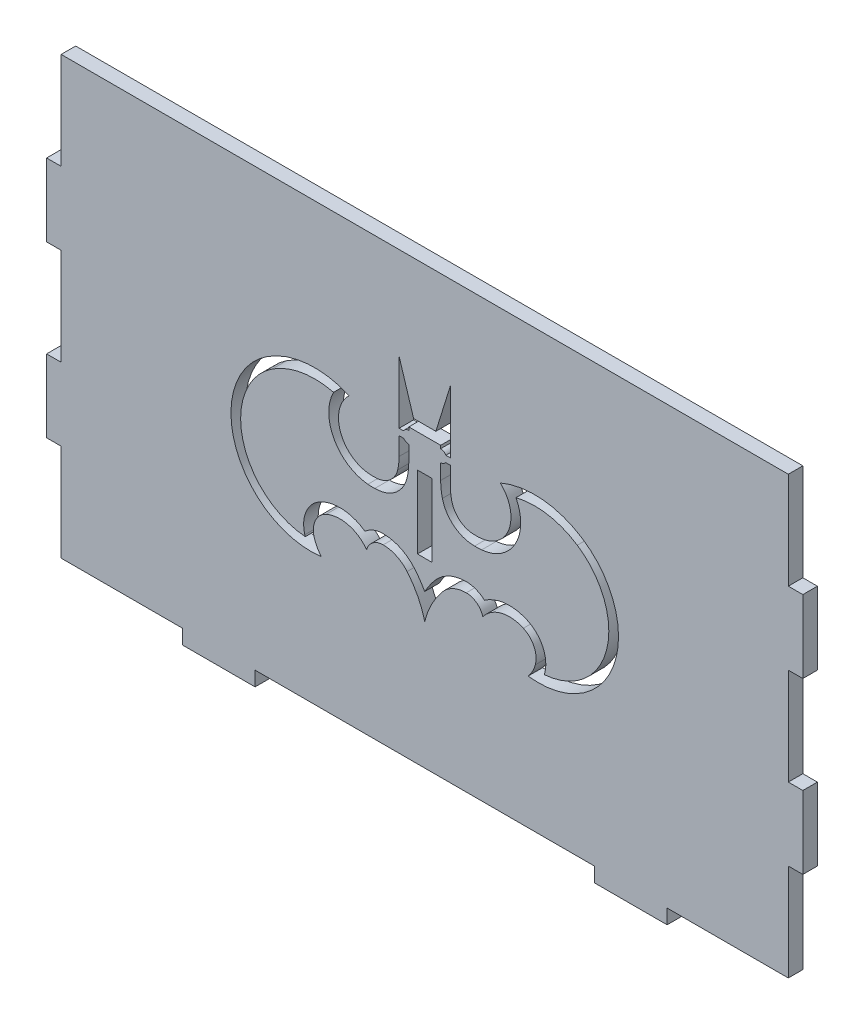
SolidWorks part; units mm, degrees
ref_plane "Front Plane" through (0, 0, 0) normal (0, 0, 1) x (1, 0, 0)
ref_plane "Top Plane" through (0, 0, 0) normal (0, 1, 0) x (1, 0, 0)
ref_plane "Right Plane" through (0, 0, 0) normal (1, 0, 0) x (0, 0, -1)
sketch "Sketch1" plane through (0, 0, 0) normal (0, 0, 1) x (1, 0, 0)
  line L0 (0, 0) -> (0, -45) construction
  line L1 (-75, 45) -> (75, 45)
  line L2 (-75, 45) -> (-75, -45)
  line L3 (-75, -45) -> (75, -45)
  line L4 (75, 45) -> (75, -45)
  line L5 (-75, 45) -> (75, -45) construction
  line L6 (-75, -45) -> (75, 45) construction
  line L7 (-75, 25) -> (-78, 25)
  line L8 (-75, 25) -> (-75, 10)
  line L9 (-75, 10) -> (-78, 10)
  line L10 (-78, 25) -> (-78, 10)
  line L11 (-50, -45) -> (-35, -45)
  line L12 (-50, -45) -> (-50, -48)
  line L13 (-50, -48) -> (-35, -48)
  line L14 (-35, -45) -> (-35, -48)
  line L15 (35, -45) -> (50, -45)
  line L16 (35, -45) -> (35, -48)
  line L17 (35, -48) -> (50, -48)
  line L18 (50, -45) -> (50, -48)
  line L19 (-75, -10) -> (-78, -10)
  line L20 (-75, -10) -> (-75, -25)
  line L21 (-75, -25) -> (-78, -25)
  line L22 (-78, -10) -> (-78, -25)
  line L23 (75, 25) -> (78, 25)
  line L24 (75, -25) -> (78, -25)
  line L25 (75, -10) -> (78, -10)
  line L26 (75, 10) -> (78, 10)
  line L27 (78, -10) -> (78, -25)
  line L28 (78, 25) -> (78, 10)
  point P0 (0, 0)
  dimension "D1" = 90
  dimension "D2" = 150
  dimension "D3" = 3
  dimension "D4" = 3
  dimension "D5" = 15
  dimension "D6" = 15
  dimension "D7" = 15
  dimension "D8" = 3
  dimension "D9" = 3
  dimension "D10" = 15
  dimension "D11" = 25
  dimension "D12" = 25
  dimension "D13" = 20
  dimension "D14" = 20
extrude "Boss-Extrude1" add sketch "Sketch1" along normal blind 3 contours L4 L1 L2 L3 | L7 L10 L9 L2 | L19 L22 L21 L2 | L28 L23 L4 L26 | L27 L25 L4 L24 | L18 L3 L16 L17 | L14 L3 L12 L13
sketch "Sketch2" plane through (0, 0, 3) normal (0, 0, 1) x (1, 0, 0)
  line L1 (-1.5, 7.5) -> (1.5, 7.5)
  line L2 (-1.5, 7.5) -> (-1.5, -7.5)
  line L3 (-1.5, -7.5) -> (1.5, -7.5)
  line L4 (1.5, 7.5) -> (1.5, -7.5)
  line L5 (-1.5, 7.5) -> (1.5, -7.5) construction
  line L6 (-1.5, -7.5) -> (1.5, 7.5) construction
  point P0 (0, 0)
  dimension "D1" = 3
  dimension "D2" = 15
extrude "Cut-Extrude1" cut sketch "Sketch2" against normal blind 10
sketch "Sketch6" plane through (0, 0, 3) normal (0, 0, 1) x (1, 0, 0)
  line L0 (600.1171, 1058.2145) -> (3160.1171, 1058.2145) construction
  line L1 (0, 13.3159) -> (0, -20.692) construction
  line L2 (2.2954, 16.3119) -> (-2.2954, 16.3119)
  line L3 (-2.2954, 16.3119) -> (-5.2905, 25.9351)
  line L4 (-5.2905, 25.9351) -> (-5.2859, 8.028)
  line L5 (5.2905, 25.9351) -> (5.2859, 8.028)
  line L6 (2.2954, 16.3119) -> (5.2905, 25.9351)
  line L7 (-3.2875, 14.3119) -> (-3.2859, 8.0285)
  line L8 (-3.2875, 14.3119) -> (-3.2875, 14.3119)
  line L9 (3.2875, 14.3119) -> (-3.2875, 14.3119)
  line L10 (3.2875, 14.3119) -> (3.2875, 14.3119)
  line L11 (3.2875, 14.3119) -> (3.2859, 8.0285)
  line L12 (5.2872, 11.7393) -> (4.3174, 11.7393)
  line L13 (-5.2872, 13.0657) -> (-4.3174, 13.0657)
  line L14 (-5.2872, 13.0657) -> (-5.2872, 11.7393)
  line L15 (-5.2872, 11.7393) -> (-4.3174, 11.7393)
  line L16 (-4.3174, 13.0657) -> (-4.3174, 11.7393)
  line L17 (4.3174, 13.0657) -> (4.3174, 11.7393)
  line L18 (5.2872, 13.0657) -> (5.2872, 11.7393)
  line L19 (5.2872, 13.0657) -> (4.3174, 13.0657)
  arc A0 (-5.2859, 8.028) -> (-5.5855, 5.465) centre (-16.3735, 8.0252) cw
  arc A1 (-15.5851, 13.7349) -> (-11.5488, 1.8385) centre (-10.9171, 8.6857) ccw
  arc A2 (-11.5488, 1.8385) -> (-10.3252, 1.8143) centre (-10.77, 10.2804) ccw
  arc A3 (-10.3252, 1.8143) -> (-5.5855, 5.465) centre (-10.2059, 6.5615) ccw
  arc A4 (-21.3283, -17.8931) -> (-32.5797, 12.2221) centre (-23.4791, -1.5373) cw
  arc A5 (-32.5797, 12.2221) -> (-15.5851, 13.7349) centre (-22.6831, -2.7407) cw
  arc A6 (3.6332, -11.7) -> (0, -18.7925) centre (17.2705, -23.1626) ccw
  arc A7 (-21.3283, -17.8931) -> (-22.8135, -15.1386) centre (-16.0059, -13.2456) cw
  arc A8 (-22.8135, -15.1386) -> (-20.3556, -9.8402) centre (-18.4746, -13.9321) cw
  arc A9 (-20.3556, -9.8402) -> (-11.9848, -11.9562) centre (-17.4826, -16.0901) cw
  arc A10 (-11.9848, -11.9562) -> (-8.5667, -9.3989) centre (-8.5704, -12.9569) cw
  arc A11 (-8.5667, -9.3989) -> (-3.6332, -11.7) centre (-8.5733, -15.8523) cw
  arc A12 (-3.6332, -11.7) -> (0, -18.7925) centre (-17.2705, -23.1626) cw
  arc A13 (8.5667, -9.3989) -> (3.6332, -11.7) centre (8.5733, -15.8523) ccw
  arc A14 (11.9848, -11.9562) -> (8.5667, -9.3989) centre (8.5704, -12.9569) ccw
  arc A15 (20.3556, -9.8402) -> (11.9848, -11.9562) centre (17.4826, -16.0901) ccw
  arc A16 (22.8135, -15.1386) -> (20.3556, -9.8402) centre (18.4746, -13.9321) ccw
  arc A17 (21.3283, -17.8931) -> (22.8135, -15.1386) centre (16.0059, -13.2456) ccw
  arc A18 (32.5797, 12.2221) -> (15.5851, 13.7349) centre (22.6831, -2.7407) ccw
  arc A19 (21.3283, -17.8931) -> (32.5797, 12.2221) centre (23.4791, -1.5373) ccw
  arc A20 (10.3252, 1.8143) -> (5.5855, 5.465) centre (10.2059, 6.5615) cw
  arc A21 (11.5488, 1.8385) -> (10.3252, 1.8143) centre (10.77, 10.2804) cw
  arc A22 (15.5851, 13.7349) -> (11.5488, 1.8385) centre (10.9171, 8.6857) cw
  arc A23 (5.2859, 8.028) -> (5.5855, 5.465) centre (16.3735, 8.0252) ccw
  arc A24 (2.1022, -10.4131) -> (0, -13.4488) centre (17.2705, -23.1626) ccw
  arc A25 (-2.1022, -10.4131) -> (0, -13.4488) centre (-17.2705, -23.1626) cw
  arc A26 (-8.5646, -7.3989) -> (-2.1022, -10.4131) centre (-8.5733, -15.8523) cw
  arc A27 (-12.3277, -8.8612) -> (-8.5646, -7.3989) centre (-8.5704, -12.9569) cw
  arc A28 (-21.1909, -8.0229) -> (-12.3277, -8.8612) centre (-17.4826, -16.0901) cw
  arc A29 (-24.7404, -15.6744) -> (-21.1909, -8.0229) centre (-18.4746, -13.9321) cw
  arc A30 (-24.6475, -15.9868) -> (-24.7404, -15.6744) centre (-16.0059, -13.2456) cw
  arc A31 (-24.6475, -15.9868) -> (-31.4763, 10.5539) centre (-23.4791, -1.5373) cw
  arc A32 (-31.4763, 10.5539) -> (-18.8217, 12.724) centre (-22.6831, -2.7407) cw
  arc A33 (-18.8217, 12.724) -> (-11.7325, -0.153) centre (-10.9171, 8.6857) ccw
  arc A34 (-11.7325, -0.153) -> (-10.2951, -0.1866) centre (-10.77, 10.2804) ccw
  arc A35 (-10.2951, -0.1866) -> (-3.6396, 5.0032) centre (-10.2059, 6.5615) ccw
  arc A36 (-3.2859, 8.0285) -> (-3.6396, 5.0032) centre (-16.3735, 8.0252) cw
  arc A37 (3.2859, 8.0285) -> (3.6396, 5.0032) centre (16.3735, 8.0252) ccw
  arc A38 (10.2951, -0.1866) -> (3.6396, 5.0032) centre (10.2059, 6.5615) cw
  arc A39 (11.7325, -0.153) -> (10.2951, -0.1866) centre (10.77, 10.2804) cw
  arc A40 (18.8217, 12.724) -> (11.7325, -0.153) centre (10.9171, 8.6857) cw
  arc A41 (31.4763, 10.5539) -> (18.8217, 12.724) centre (22.6831, -2.7407) ccw
  arc A42 (24.6475, -15.9868) -> (31.4763, 10.5539) centre (23.4791, -1.5373) ccw
  arc A43 (24.6475, -15.9868) -> (24.7404, -15.6744) centre (16.0059, -13.2456) ccw
  arc A44 (24.7404, -15.6744) -> (21.1909, -8.0229) centre (18.4746, -13.9321) ccw
  arc A45 (21.1909, -8.0229) -> (12.3277, -8.8612) centre (17.4826, -16.0901) ccw
  arc A46 (12.3277, -8.8612) -> (8.5646, -7.3989) centre (8.5704, -12.9569) ccw
  arc A47 (8.5646, -7.3989) -> (2.1022, -10.4131) centre (8.5733, -15.8523) ccw
  circle A48 centre (-3.287, 12.4469) radius 1.25
  circle A49 centre (3.287, 12.4469) radius 1.25
  point P6 (0, -3.6881)
  point P21 (-5.8454, -10.0038)
  point P62 (0, 16.3119)
  dimension "D2" = 2.5
  dimension "D1" = 20
extrude "Cut-Extrude5" cut sketch "Sketch6" against normal blind 10 contours A49 L11 A37 A38 A39 A40 A41 A42 A43 A44 A45 A46 A47 A24 A25 A26 A27 A28 A29 A30 A31 A32 A33 A34 A35 A36 L7 A48 L15 L4 A0 A3 A2 A1 A5 A4 A7 A8 A9 A10 A11 A12 A6 A13 A14 A15 A16 A17 A19 A18 A22 | A49 L19 L5 L6 L2 L3 L4 L13 A48 L7 L9 L11
